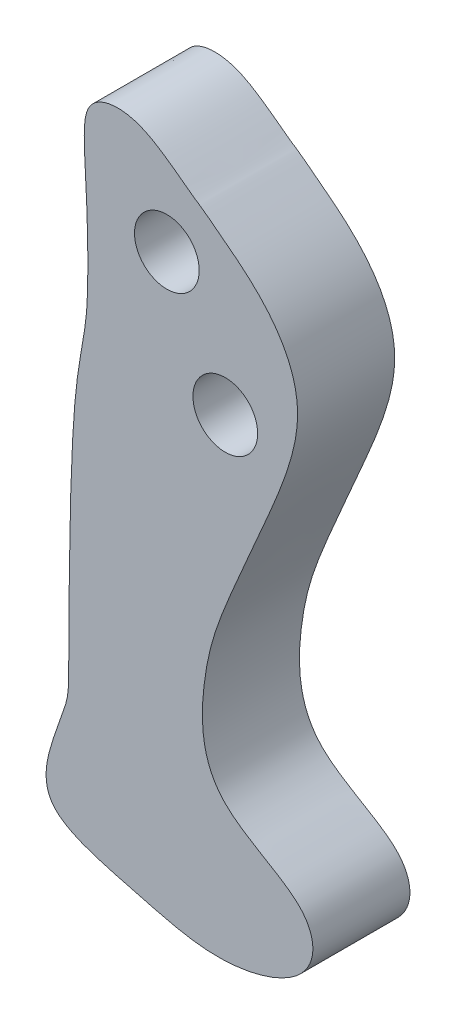
SolidWorks part; units mm, degrees
ref_plane "Спереди" through (0, 0, 0) normal (0, 0, 1) x (1, 0, 0)
ref_plane "Сверху" through (0, 0, 0) normal (0, 1, 0) x (1, 0, 0)
ref_plane "Справа" through (0, 0, 0) normal (1, 0, 0) x (0, 0, -1)
other "Configuration Table"
sketch "Sketch1" plane through (0, 0, 0) normal (0, 0, 1) x (1, 0, 0)
  circle A1 centre (-10.3833, -10.3396) radius 1
  circle A2 centre (-8.5778, -13.801) radius 1
  spline S0 degree 3 poles (-9.5423, -8.4855) (-9.3636, -8.5799) (-9.0828, -8.7868) (-7.7638, -9.8062) (-5.5635, -11.8251) (-7.4974, -16.4437) (-8.6045, -18.8884) (-9.3167, -20.9357) (-9.3636, -24.3527) (-5.7518, -25.6042) (-5.7454, -27.8475) (-8.6869, -28.6904) (-11.6, -27.8782) (-14.534, -27.1837) (-13.3788, -23.3966) (-13.4331, -24.3495) (-13.3566, -15.3931) (-13.0851, -14.893) (-12.7904, -12.7268) (-12.8556, -9.4232) (-13.0907, -7.4617) (-11.5783, -7.0663) (-10.1912, -7.9513) (-9.5423, -8.4855) (-9.3636, -8.5799) (-9.0828, -8.7868) knots -0.226569 -0.130137 -0.013014 0 0.050899 0.061631 0.107324 0.135996 0.171721 0.202521 0.228308 0.25224 0.273407 0.297554 0.312974 0.334313 0.353623 0.411232 0.432127 0.557323 0.577557 0.634468 0.705775 0.773431 0.869863 0.986986 1 1.050899 1.061631 1.107324 only from (-9.3936, -8.5661) to (-9.3936, -8.5661)
  point P1 (-13.6159, -1.6684)
  point P3 (-10.3833, -5.2238)
  point P5 (-12.8161, -7.7301)
  point P6 (0, 0)
  point P7 (-8.3749, -9.335)
  point P8 (-10.3833, -7.8518)
  point P9 (-11.8048, -7.2493)
  point P10 (-9.2555, -8.6398)
  point P11 (-9.3936, -8.5661)
  point P12 (-13.8888, -25.1068)
  dimension "D2" = 2
  dimension "D1" = 3.904
extrude "Boss-Extrude1" add sketch "Sketch1" along normal blind 3
equation "\"R small\"= 2"
equation "\"R big\"= 4"
equation "\"width\"= 0.6"
equation "\"border width\"= 1"
equation "\"D2@Sketch1\"=\"R small\""
